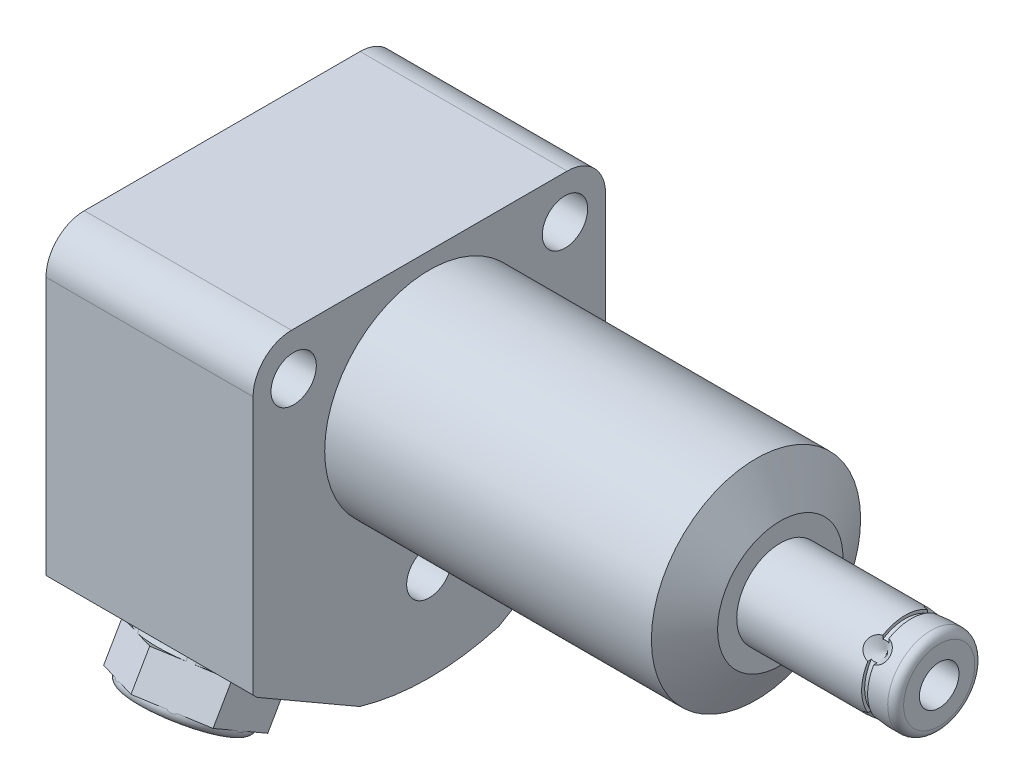
SolidWorks part; units mm, degrees
material "Alloy Steel"
ref_plane "Front Plane" through (0, 0, 0) normal (0, 0, 1) x (1, 0, 0)
ref_plane "Top Plane" through (0, 0, 0) normal (0, 1, 0) x (1, 0, 0)
ref_plane "Right Plane" through (0, 0, 0) normal (1, 0, 0) x (0, 0, -1)
sketch "Sketch1" plane through (0, 0, 0) normal (1, 0, 0) x (0, 0, -1)
  line L0 (-22.5044, 15.494) -> (-22.5044, -22.3968)
  line L1 (-21.968, -22.9231) -> (-8.868, -30.4864)
  line L2 (8.868, -30.4864) -> (21.968, -22.9231)
  line L3 (22.5044, -22.3968) -> (22.5044, 15.494)
  line L4 (22.5044, 15.494) -> (-22.5044, 15.494)
  line L5 (0, -34.1122) -> (0, 17.8562) construction
  line L6 (-36.4519, 0) -> (54.4719, 0) construction
  arc A0 (-8.868, -30.4864) -> (8.868, -30.4864) centre (0, 0) ccw
  arc A1 (-22.5044, -22.3968) -> (-21.968, -22.9231) centre (0, 0) ccw
  arc A2 (21.968, -22.9231) -> (22.5044, -22.3968) centre (0, 0) ccw
  dimension "D6" = 31.75
  dimension "D1" = 45.0088
  dimension "D2" = 30.836
  dimension "D3" = 45.0088
  dimension "D4" = 15.494
  dimension "D5" = 30
extrude "Extrude1" add sketch "Sketch1" along normal blind 44.8056 and the other way blind 26.4414
sketch "Sketch2" plane through (0, 0, 0) normal (1, 0, 0) x (0, 0, -1)
  line L6 (22.5044, 15.494) -> (-22.5044, 15.494)
  line L7 (-22.5044, 15.494) -> (-22.5044, -22.3968)
  line L8 (-21.968, -22.9231) -> (-8.868, -30.4864)
  line L9 (8.868, -30.4864) -> (21.968, -22.9231)
  line L10 (22.5044, -22.3968) -> (22.5044, 15.494)
  line L11 (22.5044, 15.494) -> (-22.5044, 15.494)
  line L12 (-22.5044, 15.494) -> (-22.5044, -22.3968)
  line L13 (-21.968, -22.9231) -> (-8.868, -30.4864)
  line L14 (8.868, -30.4864) -> (21.968, -22.9231)
  line L15 (22.5044, -22.3968) -> (22.5044, 15.494)
  circle A0 centre (0, 0) radius 13.3604
  arc A4 (-22.5044, -22.3968) -> (-21.968, -22.9231) centre (0, 0) ccw
  arc A5 (-8.868, -30.4864) -> (8.868, -30.4864) centre (0, 0) ccw
  arc A6 (21.968, -22.9231) -> (22.5044, -22.3968) centre (0, 0) ccw
  arc A7 (-22.5044, -22.3968) -> (-21.968, -22.9231) centre (0, 0) ccw
  arc A8 (-8.868, -30.4864) -> (8.868, -30.4864) centre (0, 0) ccw
  arc A9 (21.968, -22.9231) -> (22.5044, -22.3968) centre (0, 0) ccw
  dimension "D2" = 26.7208
  dimension "D1" = 0
extrude "Cut-Extrude1" cut sketch "Sketch2" along normal up to next
sketch "Sketch3" plane through (0, 0, 0) normal (0, 0, 1) x (1, 0, 0)
  line L0 (41.7113, 13.3604) -> (44.8056, 8.001)
  line L1 (23.3045, 0) -> (44.9603, 0) construction
  line L2 (44.8056, 13.3604) -> (44.8056, 8.001)
  line L3 (44.8056, 13.3604) -> (41.7113, 13.3604)
  line L4 (44.8056, -13.3604) -> (44.8056, 13.3604) construction
  line L5 (44.8056, 13.3604) -> (0, 13.3604) construction
  dimension "D1" = 30
  dimension "D2" = 16.002
revolve "Cut-Revolve1" cut sketch "Sketch3" angle 360 about L1
ref_plane "Plane19" through (0, 0, 10.49) normal (0, 0, 1) x (1, 0, 0)
sketch "S2D0002" plane through (-24.9936, -18.1864, 10.49) normal (0, 0, 1) x (0, 1, 0)
  line L0 (3.2512, 0) -> (5.7023, 0)
  line L1 (3.2512, 0) -> (3.2512, -2.9972)
  line L2 (3.2512, -2.9972) -> (1.2446, -2.9972)
  line L3 (1.2446, -2.9972) -> (1.2446, -11.9888)
  line L4 (1.2446, -11.9888) -> (0, -11.9888)
  line L5 (0, -11.9888) -> (0, 1.4478)
  line L6 (0, -23.5585) -> (0, 0.5994) construction
  line L7 (5.7023, 0) -> (5.7023, 1.4478)
  line L8 (33.6804, 1.4478) -> (-4.2104, 1.4478) construction
  line L9 (5.7023, 1.4478) -> (0, 1.4478)
  dimension "D1" = 1.4478
  dimension "D2" = 18.1864
  dimension "D3" = 11.4046
  dimension "D4" = 6.5024
  dimension "D5" = 2.4892
  dimension "D6" = 8.9916
  dimension "D7" = 2.9972
revolve "Cut-Revolve2" cut sketch "S2D0002" angle 360 about L6
ref_plane "Plane20" through (-12.9286, 0, 0) normal (1, 0, 0) x (0, 0, -1)
sketch "Sketch6" plane through (-12.9286, 0, 0) normal (1, 0, 0) x (0, 0, -1)
  line L0 (-19.5804, -24.0083) -> (-22.4357, -22.3598)
  line L1 (-19.5804, -24.0083) -> (-19.5169, -23.8983)
  line L2 (-19.5169, -23.8983) -> (-18.7883, -23.7031)
  line L3 (-18.7883, -23.7031) -> (-13.8353, -15.1242)
  line L4 (-13.8353, -15.1242) -> (-10.0078, -17.334)
  line L5 (-10.0078, -17.334) -> (-15.418, -26.7048)
  line L6 (-6.5499, -11.3447) -> (3.1494, 5.455) construction
  line L7 (-22.4357, -22.3598) -> (-22.5627, -22.5798)
  line L8 (-21.968, -22.9231) -> (-8.868, -30.4864) construction
  line L9 (-22.5627, -22.5798) -> (-15.418, -26.7048)
  line L10 (-21.968, -22.9231) -> (-8.868, -30.4864) construction
  dimension "D1" = 0.254
  dimension "D2" = 16.5
  dimension "D3" = 45
  dimension "D4" = 0.6604
  dimension "D5" = 9.906
  dimension "D6" = 8.8392
  dimension "D7" = 10.5664
  dimension "D8" = 0.127
revolve "Cut-Revolve4" cut sketch "Sketch6" angle 360 about L6
mirror "Mirror1" about plane through (0, 0, 0) normal (0, 0, 1) of "Cut-Revolve2", "Cut-Revolve4"
sketch "Sketch7" plane through (0, 0, 0) normal (0, 0, 1) x (1, 0, 0)
  line L0 (44.8056, 0) -> (44.8056, 5.5563)
  line L1 (44.8056, 5.5563) -> (64.0846, 5.5563)
  line L2 (65.1006, 4.5403) -> (65.1006, 0)
  line L3 (65.1006, 0) -> (44.8056, 0)
  line L4 (4.9931, 0) -> (66.1154, 0) construction
  line L5 (44.8056, -8.001) -> (44.8056, 8.001) construction
  line L6 (-26.4414, 15.494) -> (-26.4414, -22.3968) construction
  arc A0 (65.1006, 4.5403) -> (64.0846, 5.5563) centre (64.0846, 4.5403) ccw
  point P0 (44.8056, 0)
  dimension "D3" = 1.016
  dimension "D1" = 91.542
  dimension "D2" = 11.1125
revolve "Revolve1" add sketch "Sketch7" angle 360 about L4
sketch "S2D0001" plane through (0, 0, 0) normal (0, 0, 1) x (1, 0, 0)
  line L0 (65.1006, -2.5273) -> (54.9406, -2.5273)
  line L1 (54.9406, -2.5273) -> (53.422, 0)
  line L2 (65.1006, -2.5273) -> (65.1006, 0)
  line L3 (65.1006, 0) -> (53.422, 0)
  line L4 (-2.5273, 0) -> (-28.8062, 0) construction
  line L5 (65.1006, -4.5403) -> (65.1006, 4.5403) construction
  dimension "D1" = 5.0546
  dimension "D2" = 10.16
  dimension "D3" = 59
revolve "Cut-Revolve8" cut sketch "S2D0001" angle 360 about L4
sketch3d "3DSketch1" plane through (0, 0, 0) normal (0, 0, 1) x (1, 0, 0)
  dimension "D1" = 45
sketch "Sketch9" plane through (0, 0, 0) normal (0, -0.7071, 0.7071) x (1, 0, 0)
  line L0 (61.1382, -5.5563) -> (59.5507, -5.5563)
  line L1 (59.5507, -5.5563) -> (61.1382, -3.9688)
  line L2 (61.1382, -5.5563) -> (61.1382, -3.9688)
  line L3 (61.1382, -6.2534) -> (61.1382, 0.0794) construction
  line L4 (44.8056, -5.5563) -> (64.0846, -5.5563) construction
  line L5 (65.1006, -4.5403) -> (65.1006, 4.5403) construction
  dimension "D1" = 3.9624
  dimension "D2" = 45
  dimension "D3" = 3.175
revolve "Cut-Revolve9" cut sketch "Sketch9" angle 360 about L3
sketch "Sketch11" plane through (0, 0, 0) normal (0, 1, 0) x (1, 0, 0)
  line L0 (61.5192, -5.5563) -> (61.5192, -5.1753)
  line L1 (61.5192, -5.1753) -> (60.7572, -5.1753)
  line L2 (60.7572, -5.1753) -> (60.7572, -5.5563)
  line L3 (60.7572, -5.5563) -> (61.5192, -5.5563)
  line L4 (0, 0) -> (83.4312, 0) construction
  line L6 (44.8056, -5.5563) -> (64.0846, -5.5563) construction
  line L7 (61.1382, 2.8063) -> (61.1382, -20.2865) construction
  dimension "D1" = 0.762
  dimension "D2" = 0.381
revolve "Cut-Revolve5" cut sketch "Sketch11" angle 360 about L4
sketch "Sketch12" plane through (0, -26.4848, 15.291) normal (0, -0.866, 0.5) x (1, 0, 0)
  line L8 (-12.9286, -8.0656) -> (-5.9436, -4.0328)
  line L9 (-5.9436, -4.0328) -> (-5.9436, 4.0328)
  line L10 (-5.9436, 4.0328) -> (-12.9286, 8.0656)
  line L11 (-12.9286, 8.0656) -> (-19.9136, 4.0328)
  line L12 (-19.9136, 4.0328) -> (-19.9136, -4.0328)
  line L13 (-19.9136, -4.0328) -> (-12.9286, -8.0656)
  circle A0 centre (-12.9286, 0) radius 6.985 construction
  dimension "D2" = 13.97
extrude "Extrude2" add sketch "Sketch12" along normal blind 6.78
sketch "Sketch13" plane through (-12.9286, -6.4643, -11.1965) normal (1, 0, 0) x (0, -0.866, 0.5)
  line L0 (30.582, -5.9286) -> (31.582, -5.9286)
  line L1 (31.582, -5.9286) -> (31.582, -4.6786)
  line L2 (31.582, -4.6786) -> (30.582, -4.6786)
  line L3 (30.582, -4.6786) -> (30.582, -5.9286)
  line L4 (36.362, -5.9286) -> (36.362, -4.6786)
  line L5 (36.362, -4.6786) -> (37.362, -4.6786)
  line L6 (37.362, -4.6786) -> (37.362, -6.9286)
  line L7 (30.082, -12.9286) -> (41.082, -12.9286) construction
  line L8 (20.0156, -12.9286) -> (29.9216, -12.9286) construction
  line L9 (37.362, -16.9614) -> (37.362, -20.9942) construction
  line L11 (30.582, -16.9614) -> (30.582, -20.9942) construction
  arc A0 (37.362, -6.9286) -> (36.362, -5.9286) centre (36.362, -6.9286) ccw
  dimension "D3" = 1
  dimension "D1" = 1
  dimension "D2" = 16.5
  dimension "D4" = 1
  dimension "D5" = 16.5
  dimension "D6" = 14
revolve "Cut-Revolve6" cut sketch "Sketch13" angle 360 about L7
sketch "Sketch15" plane through (-21.9964, 0, 0) normal (-1, 0, 0) x (0, 0, 1)
  circle A0 centre (10.49, -18.1864) radius 2.7432
  circle A1 centre (10.49, -18.1864) radius 3.2512 construction
  dimension "D1" = 5.4864
extrude "Extrude3" add sketch "Sketch15" along normal blind 2.9972
sketch "Sketch16" plane through (-24.9936, 0, 0) normal (-1, 0, 0) x (0, 0, 1)
  line L7 (11.9271, -18.1864) -> (11.2086, -16.9418)
  line L8 (11.2086, -16.9418) -> (9.7714, -16.9418)
  line L9 (9.7714, -16.9418) -> (9.0529, -18.1864)
  line L10 (9.0529, -18.1864) -> (9.7714, -19.431)
  line L11 (9.7714, -19.431) -> (11.2086, -19.431)
  line L12 (11.2086, -19.431) -> (11.9271, -18.1864)
  circle A0 centre (10.49, -18.1864) radius 1.2446 construction
  dimension "D1" = 2.4892
extrude "Cut-Extrude2" cut sketch "Sketch16" against normal blind 2.54
chamfer "Chamfer1" distance 0.381 angle 45 1 edges at (-24.9936, -18.1864, 13.2332)
mirror "Mirror2" about plane through (0, 0, 0) normal (0, 0, 1) of "Extrude3", "Cut-Extrude2", "Chamfer1"
sketch "Sketch21" plane through (0, 0, 10.49) normal (0, 0, 1) x (1, 0, 0)
  line L0 (-35.9744, -18.1864) -> (-17.6399, -18.1864) construction
  line L1 (-13.0048, -16.9418) -> (-21.9964, -16.9418) construction
  line L2 (-21.9964, -19.431) -> (-17.3029, -19.431) construction
  line L3 (-24.9936, -12.4841) -> (-24.9936, -23.8887) construction
  circle A0 centre (-25.8572, -13.3731) radius 0.889
  dimension "D1" = 1.778
  dimension "D2" = 9.6266
  dimension "D3" = 0.8636
revolve "Revolve4" add sketch "Sketch21" angle 360 about L0
mirror "Mirror3" about plane through (0, 0, 0) normal (0, 0, 1) of bodies 129
fillet "Fillet1" radius 4.9022 2 edges at (-13.2207, 15.494, 22.5044) (-13.2207, 15.494, -22.5044)
hole_wizard "Hole1" positions "Sketch23" profile "Sketch22" legacy end condition up to next
sketch "Sketch23" plane through (0, 0, 0) normal (1, 0, 0) x (0, 0, -1)
  line L0 (0, 0) -> (0, 19.8912) construction
  point P0 (0, -19.9898)
  point P5 (-17.3228, 10.0076)
  point P13 (17.3228, 10.0076)
  dimension "D1" = 19.9898
  dimension "D2" = 10.0076
  dimension "D3" = 17.3228
sketch "Sketch22" plane through (0, -19.9898, 0) normal (0, 1, 0) x (0, 0, -1)
  line L0 (0, 0) -> (0, 26.4414)
  line L1 (0, 26.4414) -> (2.8955, 26.4414)
  line L2 (2.8955, 26.4414) -> (2.8955, 0)
  line L3 (2.8955, 0) -> (0, 0)
  line L4 (0, 110) -> (0, -10) construction
  dimension "Diameter" = 5.791
  dimension "Depth" = 26.4414
pattern_circular "CirPattern1" count 4 over 360 about axis through (0, 0, 0) along (1, 0, 0) of "Cut-Revolve9"
